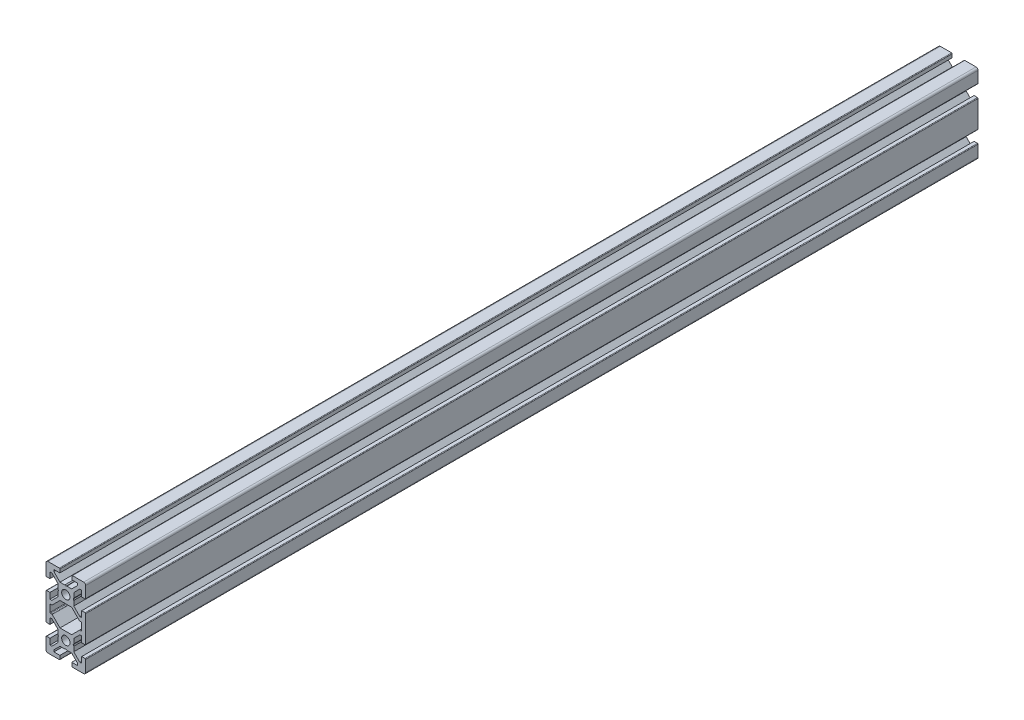
SolidWorks part; units mm, degrees
material "6061 Alloy"
ref_plane "Front Plane" through (0, 0, 0) normal (0, 0, 1) x (1, 0, 0)
ref_plane "Top Plane" through (0, 0, 0) normal (0, 1, 0) x (1, 0, 0)
ref_plane "Right Plane" through (0, 0, 0) normal (1, 0, 0) x (0, 0, -1)
sketch "Sketch1" plane through (0, 0, 0) normal (0, 0, -1) x (-1, 0, 0)
  line L0 (8, 1.7) -> (8, -1.7)
  line L1 (7.7, -2) -> (7.0636, -2)
  line L2 (6.8515, -2.0879) -> (2.9393, -6)
  line L3 (2.9393, -6) -> (-2.9393, -6)
  line L4 (-2.9393, -6) -> (-6.8515, -2.0879)
  line L5 (-7.0636, -2) -> (-7.7, -2)
  line L6 (-8, -1.7) -> (-8, 1.7)
  line L7 (-7.7, 2) -> (-7.0636, 2)
  line L8 (-6.8515, 2.0879) -> (-2.9393, 6)
  line L9 (-2.9393, 6) -> (2.9393, 6)
  line L10 (2.9393, 6) -> (6.8515, 2.0879)
  line L11 (7.0636, 2) -> (7.7, 2)
  line L12 (10, -19) -> (10, -13.3)
  line L13 (9.7, -13) -> (8, -13)
  line L14 (8, -13) -> (8, -16)
  line L15 (8, -16) -> (7.0606, -16)
  line L16 (7.0606, -16) -> (4, -12.9394)
  line L17 (4, -12.9394) -> (4, -10.5196)
  line L18 (4, -10.5196) -> (3.7, -10)
  line L19 (3.7, -10) -> (4, -9.4804)
  line L20 (4, -9.4804) -> (4, -7.0607)
  line L21 (4, -7.0607) -> (7.0607, -4)
  line L22 (7.0607, -4) -> (8, -4)
  line L23 (8, -4) -> (8, -7)
  line L24 (8, -7) -> (9.7, -7)
  line L25 (10, -6.7) -> (10, 6.7)
  line L26 (9.7, 7) -> (8, 7)
  line L27 (8, 7) -> (8, 4)
  line L28 (8, 4) -> (7.0607, 4)
  line L29 (7.0607, 4) -> (4, 7.0607)
  line L30 (4, 7.0607) -> (4, 9.4804)
  line L31 (4, 9.4804) -> (3.7, 10)
  line L32 (3.7, 10) -> (4, 10.5196)
  line L33 (4, 10.5196) -> (4, 12.9394)
  line L34 (4, 12.9394) -> (7.0606, 16)
  line L35 (7.0606, 16) -> (8, 16)
  line L36 (8, 16) -> (8, 13)
  line L37 (8, 13) -> (9.7, 13)
  line L38 (10, 13.3) -> (10, 19)
  line L39 (9, 20) -> (3.3, 20)
  line L40 (3, 19.7) -> (3, 18)
  line L41 (3, 18) -> (6, 18)
  line L42 (6, 18) -> (6, 17.0607)
  line L43 (6, 17.0607) -> (2.9393, 14)
  line L44 (2.9393, 14) -> (0.5196, 14)
  line L45 (0.5196, 14) -> (0, 13.7)
  line L46 (0, 13.7) -> (-0.5196, 14)
  line L47 (-0.5196, 14) -> (-2.9394, 14)
  line L48 (-2.9394, 14) -> (-6, 17.0607)
  line L49 (-6, 17.0607) -> (-6, 18)
  line L50 (-6, 18) -> (-3, 18)
  line L51 (-3, 18) -> (-3, 19.7)
  line L52 (-3.3, 20) -> (-9, 20)
  line L53 (-10, 19) -> (-10, 13.3)
  line L54 (-9.7, 13) -> (-8, 13)
  line L55 (-8, 13) -> (-8, 16)
  line L56 (-8, 16) -> (-7.0607, 16)
  line L57 (-7.0607, 16) -> (-4, 12.9393)
  line L58 (-4, 12.9393) -> (-4, 10.5196)
  line L59 (-4, 10.5196) -> (-3.7, 10)
  line L60 (-3.7, 10) -> (-4, 9.4804)
  line L61 (-4, 9.4804) -> (-4, 7.0607)
  line L62 (-4, 7.0607) -> (-7.0607, 4)
  line L63 (-7.0607, 4) -> (-8, 4)
  line L64 (-8, 4) -> (-8, 7)
  line L65 (-8, 7) -> (-9.7, 7)
  line L66 (-10, 6.7) -> (-10, -6.7)
  line L67 (-9.7, -7) -> (-8, -7)
  line L68 (-8, -7) -> (-8, -4)
  line L69 (-8, -4) -> (-7.0607, -4)
  line L70 (-7.0607, -4) -> (-4, -7.0607)
  line L71 (-4, -7.0607) -> (-4, -9.4804)
  line L72 (-4, -9.4804) -> (-3.7, -10)
  line L73 (-3.7, -10) -> (-4, -10.5196)
  line L74 (-4, -10.5196) -> (-4, -12.9393)
  line L75 (-4, -12.9393) -> (-7.0607, -16)
  line L76 (-7.0607, -16) -> (-8, -16)
  line L77 (-8, -16) -> (-8, -13)
  line L78 (-8, -13) -> (-9.7, -13)
  line L79 (-10, -13.3) -> (-10, -19)
  line L80 (-9, -20) -> (-3.3, -20)
  line L81 (-3, -19.7) -> (-3, -18)
  line L82 (-3, -18) -> (-6, -18)
  line L83 (-6, -18) -> (-6, -17.0607)
  line L84 (-6, -17.0607) -> (-2.9393, -14)
  line L85 (-2.9393, -14) -> (-0.5196, -14)
  line L86 (-0.5196, -14) -> (0, -13.7)
  line L87 (0, -13.7) -> (0.5196, -14)
  line L88 (0.5196, -14) -> (2.9393, -14)
  line L89 (2.9393, -14) -> (6, -17.0607)
  line L90 (6, -17.0607) -> (6, -18)
  line L91 (6, -18) -> (3, -18)
  line L92 (3, -18) -> (3, -19.7)
  line L93 (3.3, -20) -> (9, -20)
  arc A0 (7.7, 2) -> (8, 1.7) centre (7.7, 1.7) cw
  arc A1 (8, -1.7) -> (7.7, -2) centre (7.7, -1.7) cw
  arc A2 (7.0636, -2) -> (6.8515, -2.0879) centre (7.0635, -2.2999) ccw
  arc A3 (-6.8515, -2.0879) -> (-7.0636, -2) centre (-7.0636, -2.2999) ccw
  arc A4 (-7.7, -2) -> (-8, -1.7) centre (-7.7, -1.7) cw
  arc A5 (-8, 1.7) -> (-7.7, 2) centre (-7.7, 1.7) cw
  arc A6 (-7.0636, 2) -> (-6.8515, 2.0879) centre (-7.0635, 2.2999) ccw
  arc A7 (6.8515, 2.0879) -> (7.0636, 2) centre (7.0635, 2.2998) ccw
  circle A8 centre (0, -10) radius 2.1
  circle A9 centre (0, 10) radius 2.1
  arc A10 (10, -13.3) -> (9.7, -13) centre (9.7, -13.3) ccw
  arc A11 (9.7, -7) -> (10, -6.7) centre (9.7, -6.7) ccw
  arc A12 (10, 6.7) -> (9.7, 7) centre (9.7, 6.7) ccw
  arc A13 (9.7, 13) -> (10, 13.3) centre (9.7, 13.3) ccw
  arc A14 (10, 19) -> (9, 20) centre (9, 19) ccw
  arc A15 (3.3, 20) -> (3, 19.7) centre (3.3, 19.7) ccw
  arc A16 (-3, 19.7) -> (-3.3, 20) centre (-3.3, 19.7) ccw
  arc A17 (-9, 20) -> (-10, 19) centre (-9, 19) ccw
  arc A18 (-10, 13.3) -> (-9.7, 13) centre (-9.7, 13.3) ccw
  arc A19 (-9.7, 7) -> (-10, 6.7) centre (-9.7, 6.7) ccw
  arc A20 (-10, -6.7) -> (-9.7, -7) centre (-9.7, -6.7) ccw
  arc A21 (-9.7, -13) -> (-10, -13.3) centre (-9.7, -13.3) ccw
  arc A22 (-10, -19) -> (-9, -20) centre (-9, -19) ccw
  arc A23 (-3.3, -20) -> (-3, -19.7) centre (-3.3, -19.7) ccw
  arc A24 (3, -19.7) -> (3.3, -20) centre (3.3, -19.7) ccw
  arc A25 (9, -20) -> (10, -19) centre (9, -19) ccw
extrude "Boss-Extrude1" add sketch "Sketch1" along normal blind 450
